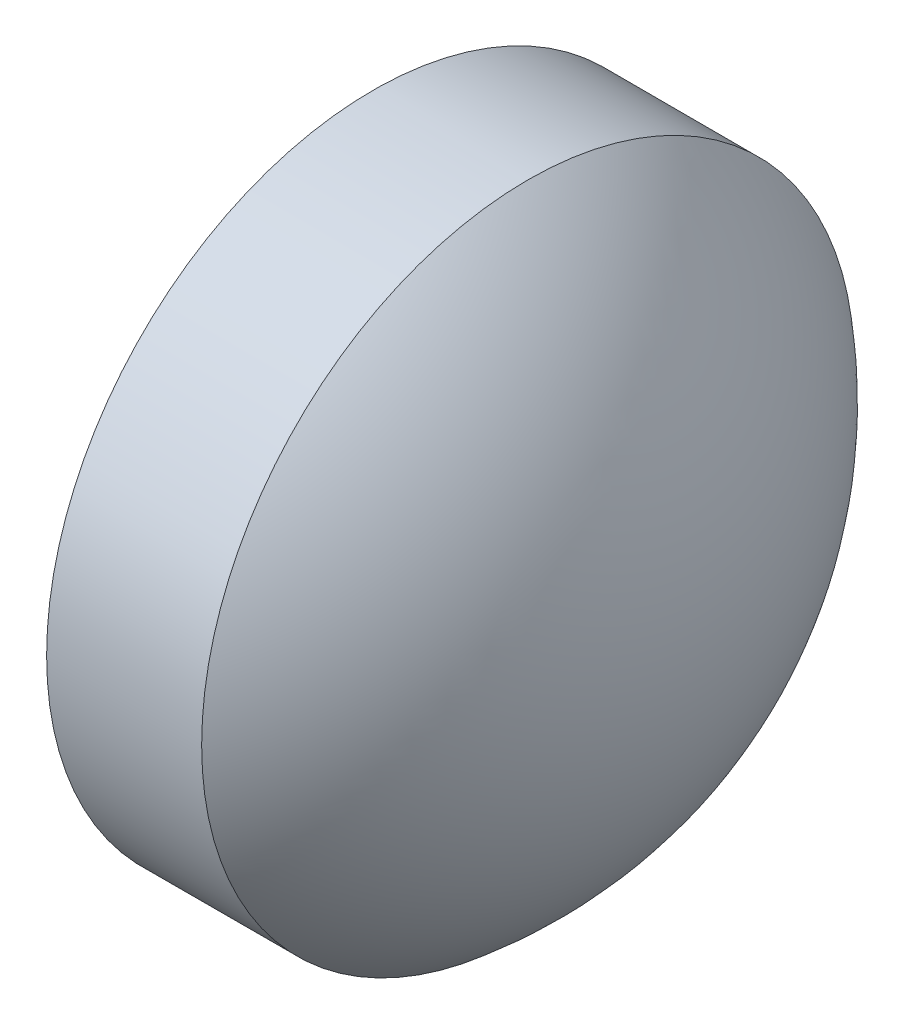
SolidWorks part; units mm, degrees
ref_plane "前视基准面" through (0, 0, 0) normal (0, 0, 1) x (1, 0, 0)
ref_plane "上视基准面" through (0, 0, 0) normal (0, 1, 0) x (1, 0, 0)
ref_plane "右视基准面" through (0, 0, 0) normal (1, 0, 0) x (0, 0, -1)
sketch "草图1" plane through (0, 0, 0) normal (0, 0, 1) x (1, 0, 0)
  line L0 (424.0583, 105.4806) -> (425.9583, 105.4806)
  line L9 (424.0583, 107.4806) -> (424.0583, 105.4806)
  line L10 (424.0583, 107.4806) -> (425.0083, 107.4806)
  line L11 (423.4284, 105.4806) -> (426.1175, 105.4806) construction
  arc A2 (425.9583, 105.4806) -> (425.0083, 107.4806) centre (423.3781, 105.4806) ccw
revolve "旋转3" add sketch "草图1" angle 360 about L11
